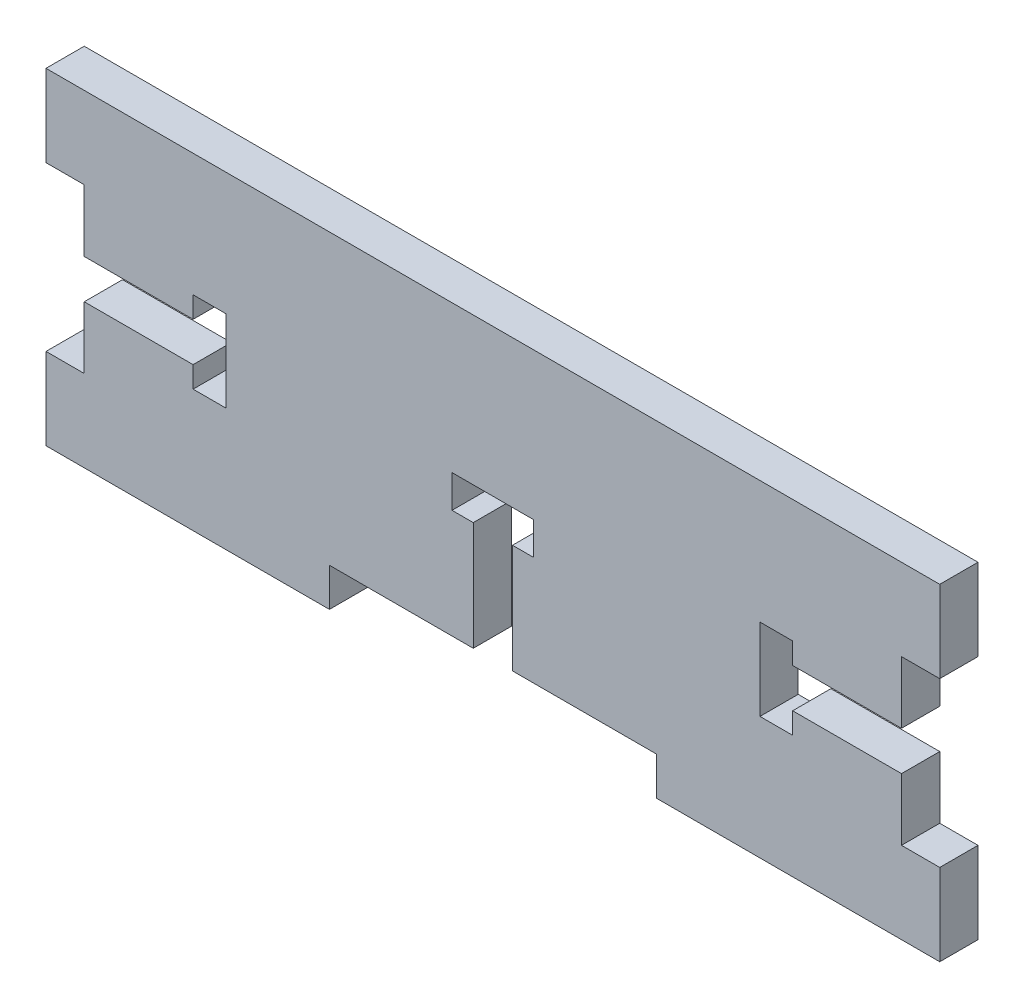
SolidWorks part; units mm, degrees
ref_plane "Front Plane" through (0, 0, 0) normal (0, 0, 1) x (1, 0, 0)
ref_plane "Top Plane" through (0, 0, 0) normal (0, 1, 0) x (1, 0, 0)
ref_plane "Right Plane" through (0, 0, 0) normal (1, 0, 0) x (0, 0, -1)
sketch "Sketch1" plane through (0, 0, 0) normal (0, 0, 1) x (1, 0, 0)
  line L0 (0, -55) -> (0, 55) construction
  line L1 (-34.7218, -12.7) -> (34.7218, -12.7)
  line L2 (-34.7218, -12.7) -> (-34.7218, 12.7)
  line L3 (-34.7218, 12.7) -> (34.7218, 12.7)
  line L4 (34.7218, -12.7) -> (34.7218, 12.7)
  line L5 (-34.7218, -12.7) -> (34.7218, 12.7) construction
  line L6 (-34.7218, 12.7) -> (34.7218, -12.7) construction
  line L7 (-34.7218, -12.7) -> (-12.7, -12.7)
  line L8 (-34.7218, -12.7) -> (-34.7218, -9.7282)
  line L9 (-34.7218, -9.7282) -> (-12.7, -9.7282)
  line L10 (-12.7, -12.7) -> (-12.7, -9.7282)
  line L11 (34.7218, -9.7282) -> (12.7, -9.7282)
  line L12 (12.7, -12.7) -> (12.7, -9.7282)
  line L13 (34.7218, -12.7) -> (12.7, -12.7)
  line L14 (34.7218, -12.7) -> (34.7218, -9.7282)
  line L15 (34.7218, -6.35) -> (31.75, -6.35)
  line L16 (-34.7218, 12.7) -> (-31.75, 12.7)
  line L17 (-34.7218, 12.7) -> (-34.7218, 6.35)
  line L18 (-34.7218, 6.35) -> (-31.75, 6.35)
  line L19 (-31.75, 12.7) -> (-31.75, 6.35)
  line L20 (-34.7218, -12.7) -> (-31.75, -12.7)
  line L21 (-34.7218, -12.7) -> (-34.7218, -6.35)
  line L22 (-34.7218, -6.35) -> (-31.75, -6.35)
  line L23 (-31.75, -12.7) -> (-31.75, -6.35)
  line L24 (31.75, -12.7) -> (31.75, -6.35)
  line L25 (34.7218, -12.7) -> (31.75, -12.7)
  line L26 (34.7218, -12.7) -> (34.7218, -6.35)
  line L27 (34.7218, 6.35) -> (31.75, 6.35)
  line L28 (31.75, 12.7) -> (31.75, 6.35)
  line L29 (34.7218, 12.7) -> (31.75, 12.7)
  line L30 (34.7218, 12.7) -> (34.7218, 6.35)
  line L31 (-31.75, 6.35) -> (-31.75, -6.35)
  line L32 (-12.7, -9.7282) -> (12.7, -9.7282)
  line L33 (31.75, 6.35) -> (31.75, -6.35)
  point P0 (0, 0)
  dimension "D1" = 69.4436
  dimension "D2" = 25.4
  dimension "D3" = 2.9718
  dimension "D4" = 25.4
  dimension "D5" = 12.7
  dimension "D6" = 2.9718
extrude "Boss-Extrude1" add sketch "Sketch1" along normal blind 2.9718 contours L33 L28 L3 L19 L31 L23 L9 L32 L11 L24 | L19 L3 L2 L18 | L9 L23 L22 L2 | L1 L23 L9 L2 | L23 L7 L10 L9 | L1 L24 L11 L12 | L24 L11 L4 L15 | L24 L13 L4 L11 | L3 L28 L27 L4
sketch "Sketch2" plane through (0, 0, 2.9718) normal (0, 0, 1) x (1, 0, 0)
  line L0 (-31.75, 0) -> (-20.7518, 0) construction
  line L1 (-31.75, 6.35) -> (-31.75, -6.35) construction
  line L2 (0, -9.7282) -> (0, 1.27) construction
  line L3 (-12.7, -9.7282) -> (12.7, -9.7282) construction
  line L4 (31.75, 0) -> (20.7518, 0) construction
  line L5 (31.75, 6.35) -> (31.75, -6.35) construction
  line L6 (-34.7218, 6.35) -> (-34.7218, 12.7) construction
  line L7 (-20.7518, 3.175) -> (-20.7518, -3.175)
  line L8 (-3.175, 1.27) -> (3.175, 1.27)
  line L9 (20.7518, 3.175) -> (20.7518, -3.175)
  line L10 (-31.75, -1.524) -> (-23.2918, -1.524)
  line L11 (1.524, -9.7282) -> (1.524, -1.27)
  line L12 (31.75, 1.524) -> (23.2918, 1.524)
  line L13 (-31.75, 1.524) -> (-23.2918, 1.524)
  line L14 (-1.524, -9.7282) -> (-1.524, -1.27)
  line L15 (31.75, -1.524) -> (23.2918, -1.524)
  line L16 (-23.2918, 3.175) -> (-23.2918, 1.524)
  line L17 (-3.175, -1.27) -> (-1.524, -1.27)
  line L18 (23.2918, 3.175) -> (23.2918, 1.524)
  line L19 (-23.2918, 3.175) -> (-20.7518, 3.175)
  line L20 (-20.7518, -3.175) -> (-23.2918, -3.175)
  line L21 (-3.175, -1.27) -> (-3.175, 1.27)
  line L23 (3.175, -1.27) -> (3.175, 1.27)
  line L24 (20.7518, 3.175) -> (23.2918, 3.175)
  line L25 (23.2918, -3.175) -> (20.7518, -3.175)
  line L26 (23.2918, -1.524) -> (23.2918, -3.175)
  line L27 (31.75, 1.524) -> (20.7518, 1.524) construction
  line L28 (1.524, -1.27) -> (3.175, -1.27)
  line L29 (23.2918, 3.175) -> (23.2918, -3.175) construction
  line L30 (31.75, -1.524) -> (20.7518, -1.524) construction
  line L31 (-1.524, -9.7282) -> (-1.524, 1.27) construction
  line L32 (-23.2918, -1.524) -> (-23.2918, -3.175)
  line L33 (-3.175, -1.27) -> (3.175, -1.27) construction
  line L34 (1.524, -9.7282) -> (1.524, 1.27) construction
  line L35 (-31.75, 1.524) -> (-31.75, -1.524)
  line L36 (-23.2918, 3.175) -> (-23.2918, -3.175) construction
  line L37 (-31.75, 1.524) -> (-20.7518, 1.524) construction
  line L38 (-31.75, -1.524) -> (-20.7518, -1.524) construction
  line L39 (-1.524, -9.7282) -> (1.524, -9.7282)
  line L40 (31.75, 1.524) -> (31.75, -1.524)
  point P17 (-20.7518, 0)
  point P20 (0, 1.27)
  point P23 (20.7518, 0)
  dimension "D1" = 13.97
  dimension "D2" = 6.35
  dimension "D3" = 1.524
  dimension "D4" = 1.524
  dimension "D5" = 2.54
  dimension "D6" = 2.54
extrude "Cut-Extrude1" cut sketch "Sketch2" against normal through all
